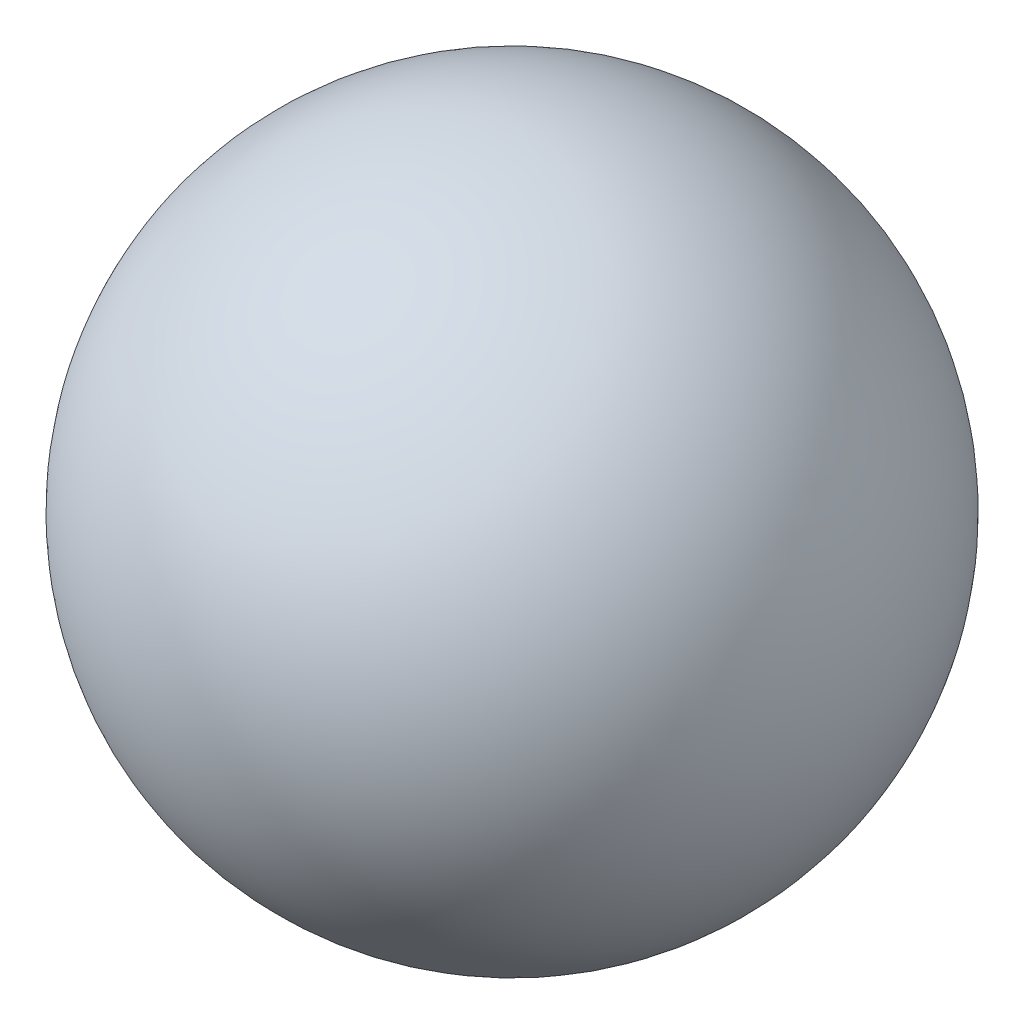
SolidWorks part; units mm, degrees
ref_plane "Front Plane" through (0, 0, 0) normal (0, 0, 1) x (1, 0, 0)
ref_plane "Top Plane" through (0, 0, 0) normal (0, 1, 0) x (1, 0, 0)
ref_plane "Right Plane" through (0, 0, 0) normal (1, 0, 0) x (0, 0, -1)
sketch "Sketch1" plane through (0, 0, 0) normal (0, 0, 1) x (1, 0, 0)
  line L0 (0.28, 0) -> (-0.28, 0)
  arc A0 (-0.28, 0) -> (0.28, 0) centre (0, 0) cw
  dimension "D1" = 0.28
revolve "Revolve1" add sketch "Sketch1" angle 360 about L0
